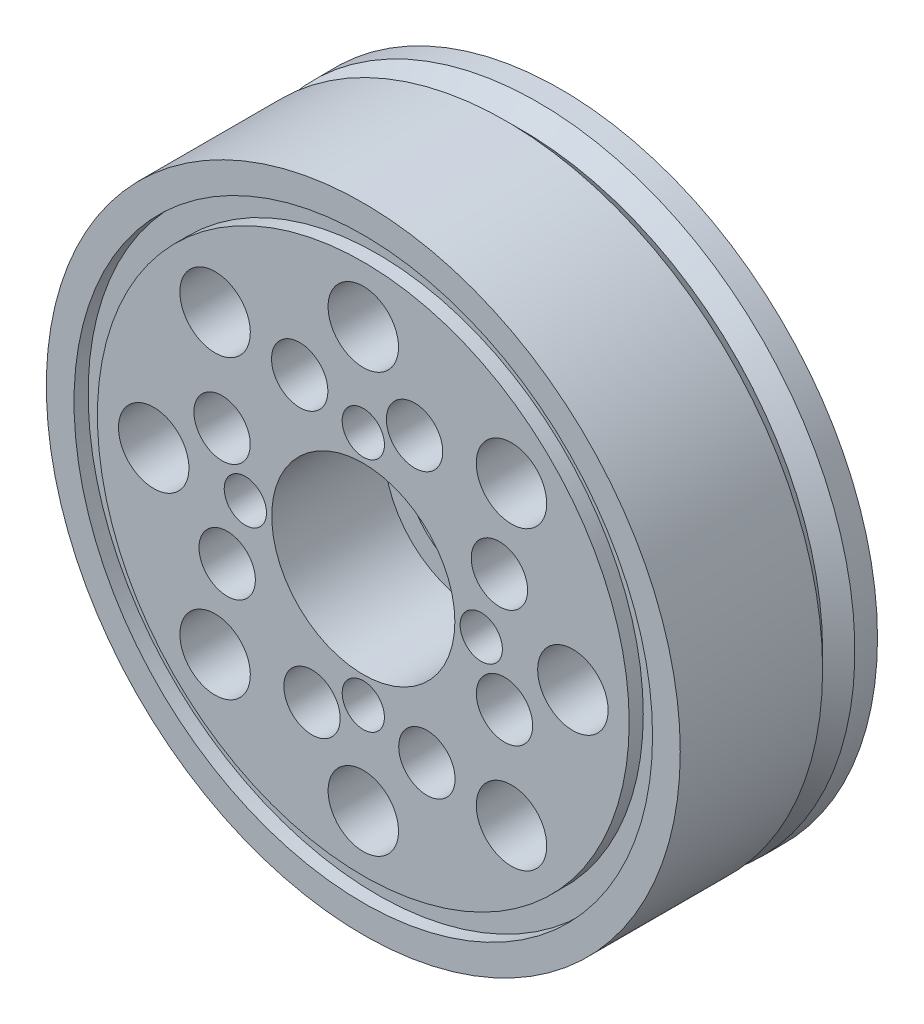
SolidWorks part; units mm, degrees
ref_plane "前视基准面" through (0, 0, 0) normal (0, 0, 1) x (1, 0, 0)
ref_plane "上视基准面" through (0, 0, 0) normal (0, 1, 0) x (1, 0, 0)
ref_plane "右视基准面" through (0, 0, 0) normal (1, 0, 0) x (0, 0, -1)
sketch "草图1" plane through (0, 0, 0) normal (0, 0, 1) x (1, 0, 0)
  circle A0 centre (0, 0) radius 22.5
extrude "凸台-拉伸1" add sketch "草图1" along normal blind 14
ref_plane "基准面1" through (0, 0, 5) normal (0, 0, 1) x (1, 0, 0)
sketch "草图4" plane through (0, 0, 14) normal (0, 0, 1) x (1, 0, 0)
  circle A0 centre (0, 0) radius 20.5336
  circle A1 centre (0, 0) radius 18.8738
extrude "切除-拉伸2" cut sketch "草图4" against normal blind 1
sketch "草图5" plane through (0, 0, 14) normal (0, 0, 1) x (1, 0, 0)
  circle A0 centre (0, 0) radius 6.5
extrude "切除-拉伸3" cut sketch "草图5" against normal blind 8
sketch "草图6" plane through (0, 0, 6) normal (0, 0, 1) x (1, 0, 0)
  circle A0 centre (0, 0) radius 5
extrude "切除-拉伸4" cut sketch "草图6" against normal blind 8
sketch "草图7" plane through (0, 0, 14) normal (0, 0, 1) x (1, 0, 0)
  circle A0 centre (0, 8.3728) radius 1.5
extrude "切除-拉伸5" cut sketch "草图7" against normal blind 5
pattern_circular "阵列(圆周)1" count 4 over 360 about axis through (0, 0, 0) along (0, 0, 1) of "切除-拉伸5"
sketch "草图8" plane through (0, 0, 14) normal (0, 0, 1) x (1, 0, 0)
  circle A0 centre (0, 14.8765) radius 2.5
extrude "切除-拉伸6" cut sketch "草图8" against normal blind 5
pattern_circular "阵列(圆周)2" count 8 over 360 about axis through (0, 0, 0) along (0, 0, 1) of "切除-拉伸6"
sketch "草图9" plane through (0, 0, 14) normal (0, 0, 1) x (1, 0, 0)
  circle A0 centre (-4.5137, 9.6618) radius 2
extrude "切除-拉伸10" cut sketch "草图9" against normal blind 5
pattern_circular "阵列(圆周)3" count 8 over 360 about axis through (0, 0, 0) along (0, 0, 1) of "切除-拉伸10"
scale "缩放比例1" bodies to scale 120 scale about centroid uniform scaling yes scale factor 1.244444
sketch "草图10" plane through (0, 0, 0) normal (1, 0, 0) x (0, 0, -1)
  line L0 (0, 0) -> (-8.777, 0)
  line L2 (-0.4, 28.0049) -> (-1.8284, 26.5766)
  line L3 (-1.8284, 26.5766) -> (-3.2568, 28.0049)
  line L4 (-3.2568, 28.0049) -> (-0.4, 28.0049)
revolve "切除-旋转1" cut sketch "草图10" angle 360 about L0
